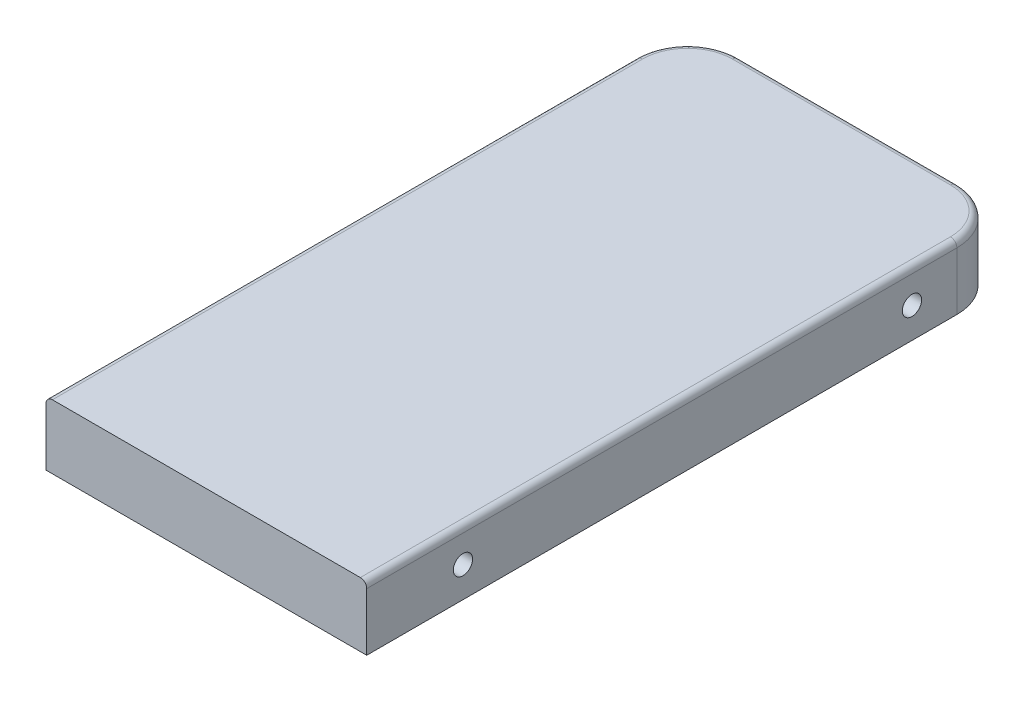
SolidWorks part; units mm, degrees
ref_plane "Front Plane" through (0, 0, 0) normal (0, 0, 1) x (1, 0, 0)
ref_plane "Top Plane" through (0, 0, 0) normal (0, 1, 0) x (1, 0, 0)
ref_plane "Right Plane" through (0, 0, 0) normal (1, 0, 0) x (0, 0, -1)
sketch "Sketch1" plane through (0, 0, 0) normal (0, 1, 0) x (1, 0, 0)
  line L1 (0, 0) -> (500, 0)
  line L2 (0, 0) -> (0, -1000)
  line L3 (0, -1000) -> (500, -1000)
  line L4 (500, 0) -> (500, -1000)
  dimension "D1" = 500
  dimension "D2" = 1000
extrude "Boss-Extrude1" add sketch "Sketch1" along normal blind 100
sketch "Sketch2" plane through (500, 0, 0) normal (1, 0, 0) x (0, 0, -1)
  line L0 (-1000, 100) -> (-1000, 0) construction
  line L1 (0, 100) -> (0, 0) construction
  circle A0 centre (-850, 47.4194) radius 15
  circle A1 centre (-150, 47.4194) radius 15
  dimension "D3" = 30
  dimension "D4" = 30
  dimension "D1" = 150
  dimension "D2" = 150
extrude "Cut-Extrude1" cut sketch "Sketch2" against normal through all
fillet "Fillet1" radius 80 2 edges at (500, 50, 0) (0, 50, 0)
fillet "Fillet2" radius 10 5 edges at (500, 100, 540) (476.5685, 100, 23.4315) (0, 100, 540) (23.4315, 100, 23.4315) (250, 100, 0)
